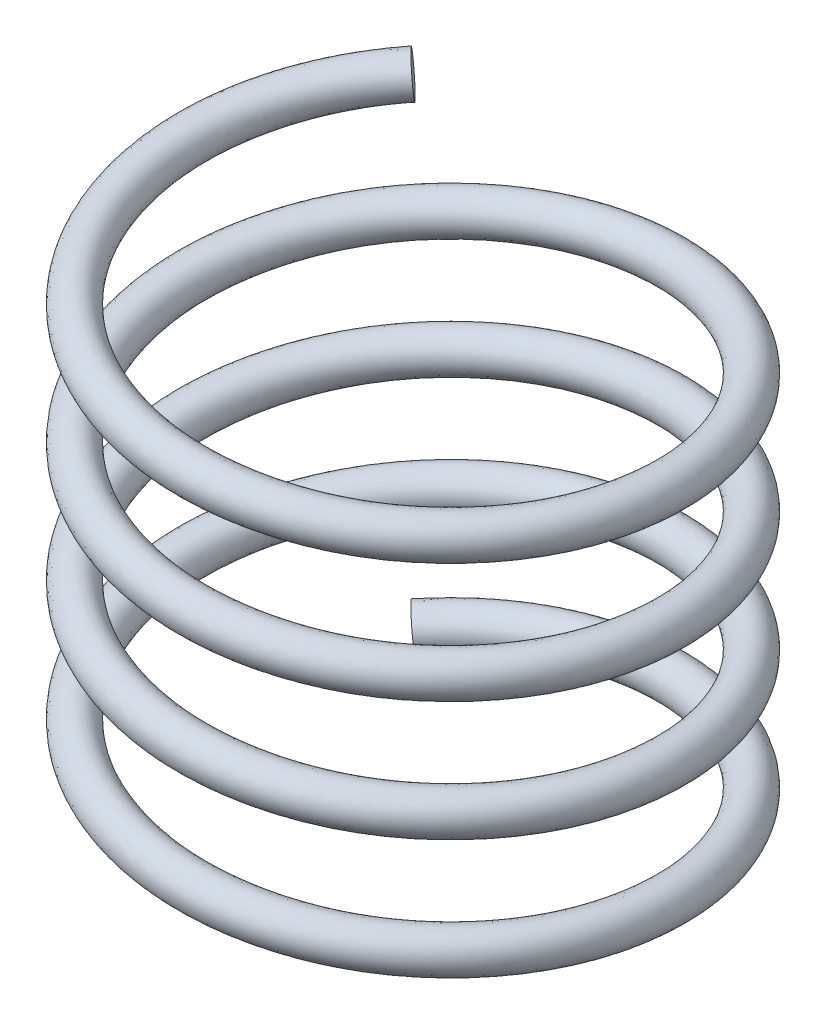
SolidWorks part; units mm, degrees
ref_plane "정면" through (0, 0, 0) normal (0, 0, 1) x (1, 0, 0)
ref_plane "윗면" through (0, 0, 0) normal (0, 1, 0) x (1, 0, 0)
ref_plane "우측면" through (0, 0, 0) normal (1, 0, 0) x (0, 0, -1)
sketch "스케치1" plane through (0, 0, 0) normal (0, 1, 0) x (1, 0, 0)
  circle A0 centre (0, 0) radius 6
  point P2 (0, 0)
  dimension "D1" = 12
curve "나선형 곡선1" pitch 3 height 12 turns 4
sweep "스윕1" add path "나선형 곡선1" circular profile diameter 1 parameters "D3"=1
